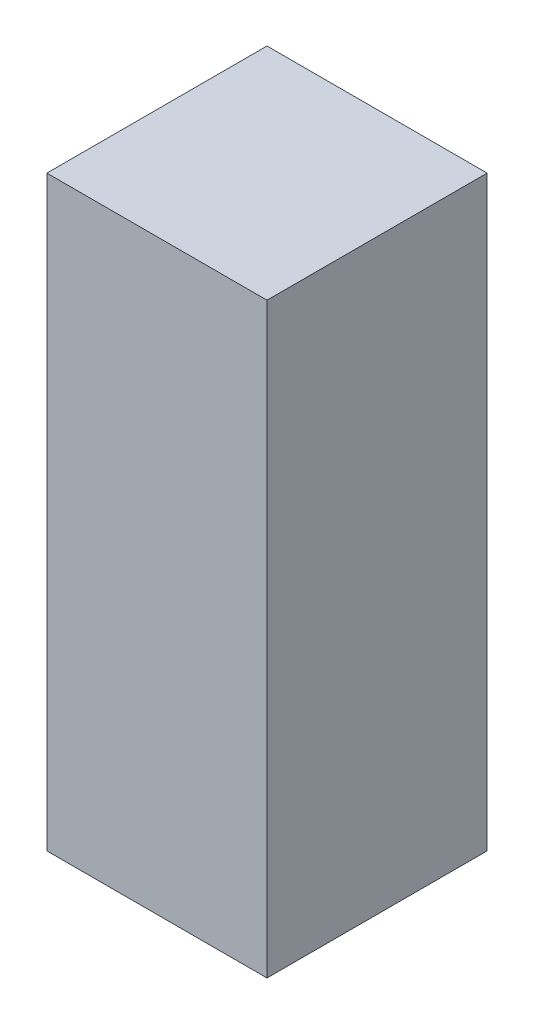
SolidWorks part; units mm, degrees
ref_plane "Front Plane" through (0, 0, 0) normal (0, 0, 1) x (1, 0, 0)
ref_plane "Top Plane" through (0, 0, 0) normal (0, 1, 0) x (1, 0, 0)
ref_plane "Right Plane" through (0, 0, 0) normal (1, 0, 0) x (0, 0, -1)
sketch "Sketch1" plane through (0, 0, 0) normal (0, 1, 0) x (1, 0, 0)
  line L1 (0, 0) -> (3, 0)
  line L2 (0, 0) -> (0, 3)
  line L3 (0, 3) -> (3, 3)
  line L4 (3, 0) -> (3, 3)
  dimension "D1" = 3
  dimension "D2" = 3
extrude "Boss-Extrude1" add sketch "Sketch1" along normal blind 8
